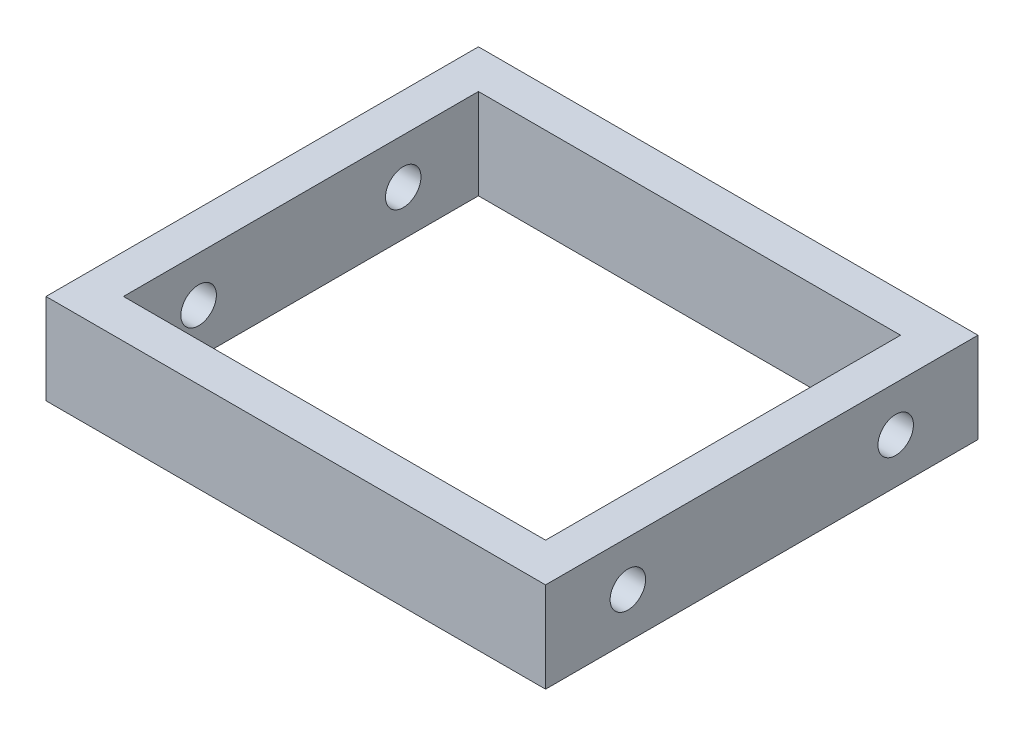
SolidWorks part; units mm, degrees
ref_plane "Front Plane" through (0, 0, 0) normal (0, 0, 1) x (1, 0, 0)
ref_plane "Top Plane" through (0, 0, 0) normal (0, 1, 0) x (1, 0, 0)
ref_plane "Right Plane" through (0, 0, 0) normal (1, 0, 0) x (0, 0, -1)
sketch "Sketch1" plane through (0, 0, 0) normal (0, 1, 0) x (1, 0, 0)
  line L1 (-32.7, -27.5) -> (32.7, -27.5)
  line L2 (-32.7, -27.5) -> (-32.7, 27.5)
  line L3 (-32.7, 27.5) -> (32.7, 27.5)
  line L4 (32.7, -27.5) -> (32.7, 27.5)
  line L5 (-32.7, -27.5) -> (32.7, 27.5) construction
  line L6 (-32.7, 27.5) -> (32.7, -27.5) construction
  line L7 (-38.7, -33.5) -> (38.7, -33.5)
  line L8 (-38.7, -33.5) -> (-38.7, 33.5)
  line L9 (-38.7, 33.5) -> (38.7, 33.5)
  line L10 (38.7, -33.5) -> (38.7, 33.5)
  line L11 (-38.7, -33.5) -> (38.7, 33.5) construction
  line L12 (-38.7, 33.5) -> (38.7, -33.5) construction
  circle A0 centre (-12.4, 0) radius 4
  circle A1 centre (53.6, 0) radius 4
  point P0 (0, 0)
  point P6 (0, 0)
  dimension "D3" = 8
  dimension "D1" = 20.3
  dimension "D2" = 14.9
  dimension "D4" = 66
  dimension "D5" = 6
  dimension "D6" = 6
  dimension "D7" = 55
  dimension "D8" = 86.3
extrude "Boss-Extrude1" add sketch "Sketch1" along normal blind 14 contours L7 L10 L9 L8 L4 L1 L2 L3
sketch "Sketch2" plane through (38.7, 0, 0) normal (1, 0, 0) x (0, 0, -1)
  line L0 (-20.75, 7) -> (20.75, 7) construction
  line L1 (33.5, 14) -> (33.5, 0) construction
  circle A0 centre (-20.75, 7) radius 2.75
  circle A1 centre (20.75, 7) radius 2.75
  point P4 (33.5, 7)
  point P5 (0, 7)
  dimension "D1" = 5.5
  dimension "D2" = 41.5
extrude "Cut-Extrude1" cut sketch "Sketch2" against normal up to surface (6 mm away) up to face at (32.7, 7, 0)
sketch "Sketch3" plane through (-32.7, 0, 0) normal (1, 0, 0) x (0, 0, -1)
  line L0 (15.85, 7) -> (-15.85, 7) construction
  line L3 (-15.85, 7) -> (-33.5, 7) construction
  line L4 (-33.5, 14) -> (-33.5, 0) construction
  circle A0 centre (15.85, 7) radius 2.75
  circle A1 centre (-15.85, 7) radius 2.75
  point P0 (0, 7)
  dimension "D2" = 5.5
  dimension "D1" = 31.7
extrude "Cut-Extrude2" cut sketch "Sketch3" against normal up to surface (6 mm away) up to face at (-38.7, 7, 0)
